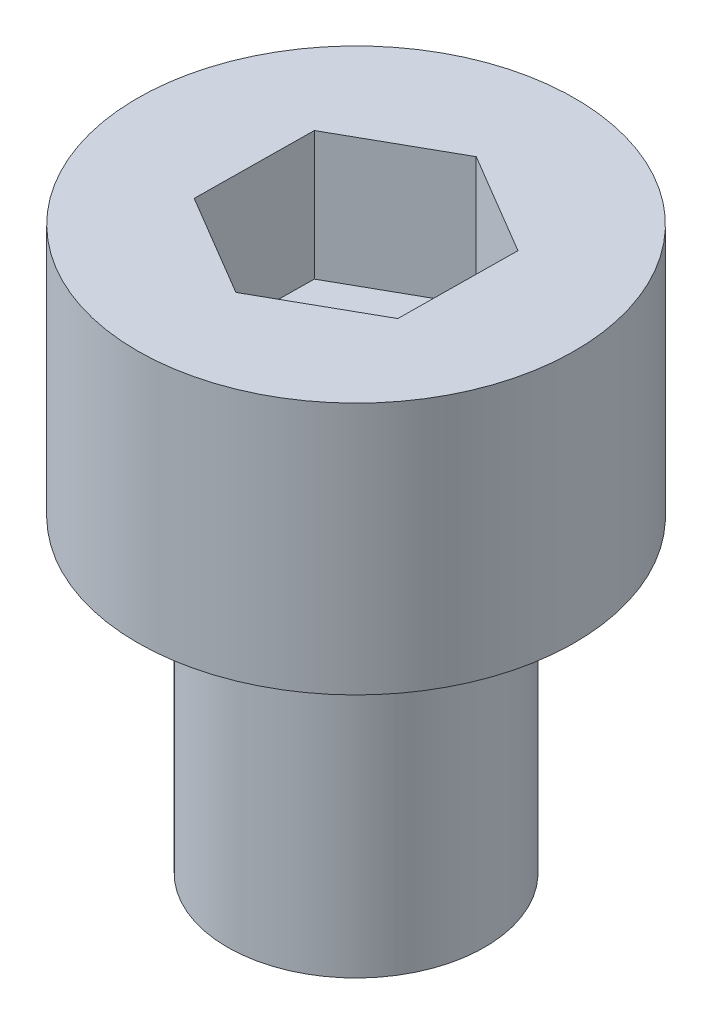
SolidWorks part; units mm, degrees
ref_plane "前视基准面" through (0, 0, 0) normal (0, 0, 1) x (1, 0, 0)
ref_plane "上视基准面" through (0, 0, 0) normal (0, 1, 0) x (1, 0, 0)
ref_plane "右视基准面" through (0, 0, 0) normal (1, 0, 0) x (0, 0, -1)
sketch "草图1" plane through (0, 0, 0) normal (0, 1, 0) x (1, 0, 0)
  circle A0 centre (0, 0) radius 2.5
  dimension "D1" = 5
extrude "凸台-拉伸1" add sketch "草图1" along normal blind 6
sketch "草图2" plane through (0, 6, 0) normal (0, 1, 0) x (1, 0, 0)
  circle A0 centre (0, 0) radius 4.25
  dimension "D1" = 8.5
extrude "凸台-拉伸2" add sketch "草图2" along normal blind 4.91
sketch "草图3" plane through (0, 10.91, 0) normal (0, 1, 0) x (1, 0, 0)
  line L1 (1.9872, -1.1765) -> (2.0125, 1.1327)
  line L2 (2.0125, 1.1327) -> (0.0253, 2.3093)
  line L3 (0.0253, 2.3093) -> (-1.9872, 1.1765)
  line L4 (-1.9872, 1.1765) -> (-2.0125, -1.1327)
  line L5 (-2.0125, -1.1327) -> (-0.0253, -2.3093)
  line L6 (-0.0253, -2.3093) -> (1.9872, -1.1765)
  circle A0 centre (0, 0) radius 2 construction
  dimension "D1" = 4
extrude "切除-拉伸1" cut sketch "草图3" against normal blind 2.5
